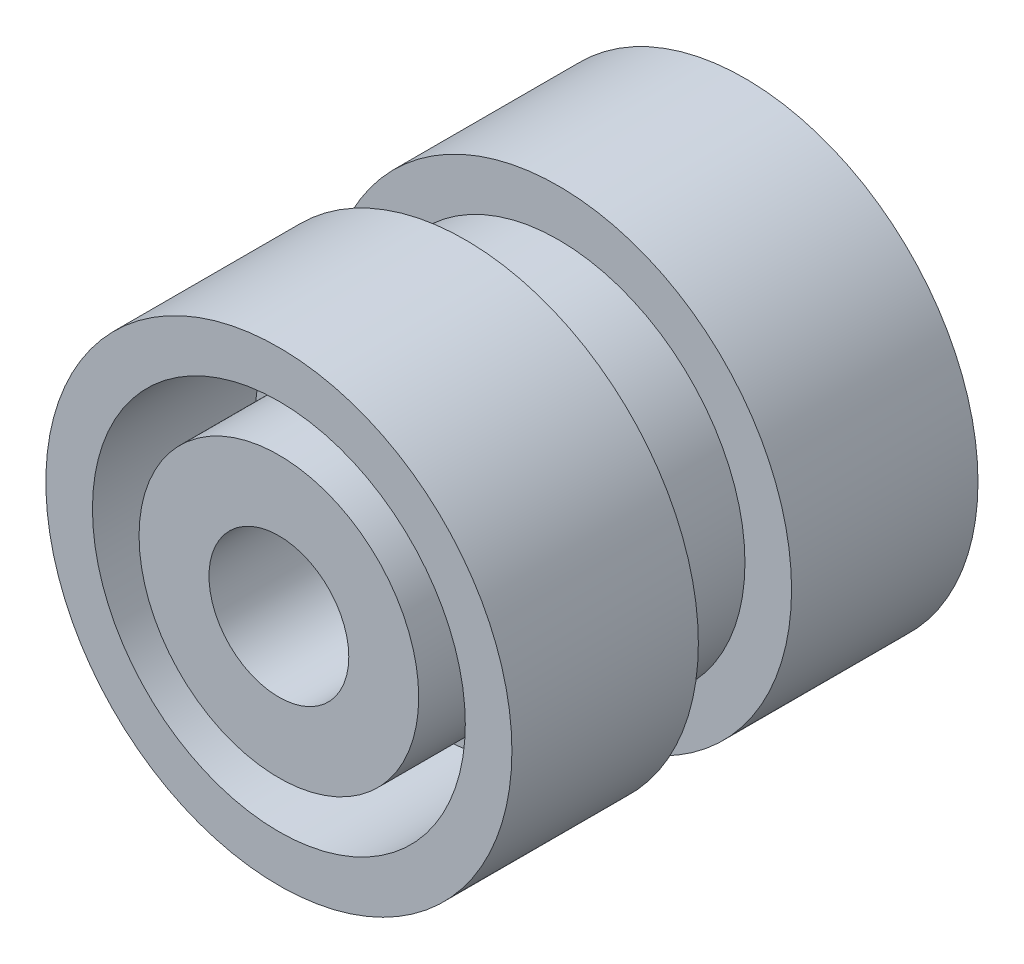
SolidWorks part; units mm, degrees
ref_plane "Front Plane" through (0, 0, 0) normal (0, 0, 1) x (1, 0, 0)
ref_plane "Top Plane" through (0, 0, 0) normal (0, 1, 0) x (1, 0, 0)
ref_plane "Right Plane" through (0, 0, 0) normal (1, 0, 0) x (0, 0, -1)
sketch "Sketch1" plane through (0, 0, 0) normal (1, 0, 0) x (0, 0, -1)
  line L0 (0, 0) -> (1.5, 0)
  line L1 (1.5, 0) -> (1.5, 4)
  line L2 (1.5, 4) -> (5, 4)
  line L3 (5, 4) -> (5, 5)
  line L4 (5, 5) -> (1, 5)
  line L5 (1, 5) -> (1, 4)
  line L6 (1, 4) -> (-1, 4)
  line L7 (-1, 4) -> (-1, 5)
  line L8 (-1, 5) -> (-5, 5)
  line L9 (-5, 5) -> (-5, 4)
  line L10 (-5, 4) -> (-1.5, 4)
  line L11 (-1.5, 4) -> (-1.5, 3)
  line L12 (-1.5, 3) -> (-5, 3)
  line L13 (-5, 3) -> (-5, 0)
  line L14 (-5, 0) -> (0, 0)
  line L15 (-8.4354, 0) -> (3.6257, 0) construction
  dimension "D1" = 5
  dimension "D2" = 3
  dimension "D3" = 3.5
  dimension "D4" = 1
  dimension "D5" = 1
  dimension "D6" = 4
  dimension "D7" = 2
  dimension "D8" = 4
  dimension "D9" = 3.5
revolve "Revolve1" add sketch "Sketch1" angle 360 about L15
sketch "Sketch8" plane through (0, 0, -1.5) normal (0, 0, -1) x (-1, 0, 0)
  line L1 (-0.5, 3.9686) -> (-0.5, 1.9365)
  line L2 (0.5, 3.9686) -> (0.5, 1.9365)
  line L3 (3.9686, -0.5) -> (1.9365, -0.5)
  line L4 (3.9686, 0.5) -> (1.9365, 0.5)
  line L5 (-0.5, -3.9686) -> (-0.5, -1.9365)
  line L6 (0.5, -3.9686) -> (0.5, -1.9365)
  line L7 (-3.9686, 0.5) -> (-1.9365, 0.5)
  line L8 (-3.9686, -0.5) -> (-1.9365, -0.5)
  arc A0 (-0.5, 1.9365) -> (-1.9365, 0.5) centre (0, 0) ccw
  arc A1 (3.9686, -0.5) -> (3.9686, 0.5) centre (0, 0) ccw
  arc A2 (0.5, -1.9365) -> (1.9365, -0.5) centre (0, 0) ccw
  arc A3 (-1.9365, -0.5) -> (-0.5, -1.9365) centre (0, 0) ccw
  arc A4 (1.9365, 0.5) -> (0.5, 1.9365) centre (0, 0) ccw
  arc A5 (-0.5, -3.9686) -> (0.5, -3.9686) centre (0, 0) ccw
  arc A6 (-3.9686, 0.5) -> (-3.9686, -0.5) centre (0, 0) ccw
  arc A7 (0.5, 3.9686) -> (-0.5, 3.9686) centre (0, 0) ccw
  point P26 (0, 0)
  dimension "D4" = 4
extrude "Boss-Extrude1" add sketch "Sketch8" along normal blind 2
sketch "Sketch9" plane through (0, 0, 5) normal (0, 0, 1) x (1, 0, 0)
  circle A0 centre (0, 0) radius 1.5
extrude "Cut-Extrude2" cut sketch "Sketch9" against normal blind 8
